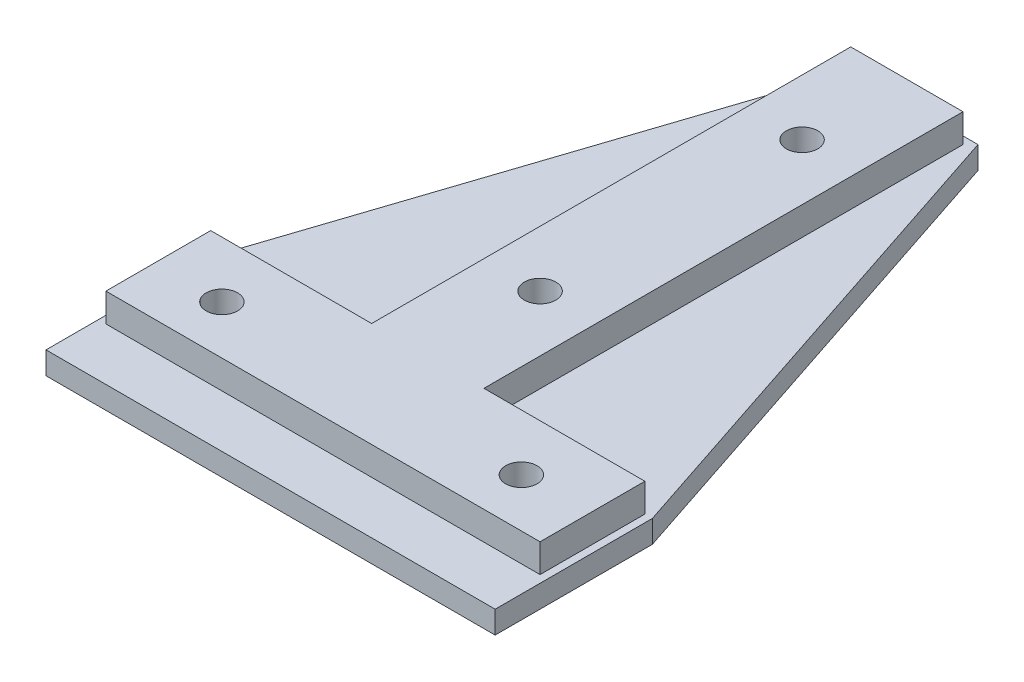
SolidWorks part; units mm, degrees
ref_plane "Front Plane" through (0, 0, 0) normal (0, 0, 1) x (1, 0, 0)
ref_plane "Top Plane" through (0, 0, 0) normal (0, 1, 0) x (1, 0, 0)
ref_plane "Right Plane" through (0, 0, 0) normal (1, 0, 0) x (0, 0, -1)
sketch "Sketch1" plane through (0, 0, 0) normal (0, 1, 0) x (1, 0, 0)
  line L0 (0, 7.5) -> (0, -50.0246) construction
  line L1 (-30, -7.5) -> (30, -7.5)
  line L2 (-30, -7.5) -> (-30, 7.5)
  line L3 (-30, 7.5) -> (30, 7.5)
  line L4 (30, -7.5) -> (30, 7.5)
  line L5 (-30, -7.5) -> (30, 7.5) construction
  line L6 (-30, 7.5) -> (30, -7.5) construction
  line L7 (-30, 0) -> (30, 0) construction
  line L8 (8.5, 7.5) -> (8.5, 72.5)
  line L9 (8.5, 7.5) -> (-8.5, 7.5)
  line L11 (8.5, 72.5) -> (-8.5, 72.5)
  line L12 (-8.5, 7.5) -> (-8.5, 72.5)
  line L13 (0, 72.5) -> (0, 7.5) construction
  line L14 (-8.5, 72.5) -> (-30, 7.5)
  line L15 (8.5, 72.5) -> (30, 7.5)
  line L17 (-30, -7.5) -> (30, -7.5)
  line L18 (-30, -7.5) -> (-30, -13.5)
  line L19 (-30, -13.5) -> (30, -13.5)
  line L20 (30, -7.5) -> (30, -13.5)
  circle A0 centre (-20, 0) radius 2.1
  circle A1 centre (20, 0) radius 2.1
  circle A2 centre (0, 57.5) radius 2.1
  circle A3 centre (0, 22.5) radius 2.1
  point P0 (0, 0)
  dimension "D3" = 4.2
  dimension "D4" = 10
  dimension "D6" = 4.2
  dimension "D7" = 15
  dimension "D8" = 4.2
  dimension "D9" = 15
  dimension "D1" = 60
  dimension "D2" = 15
  dimension "D5" = 65
  dimension "D10" = 6
extrude "Boss-Extrude1" add sketch "Sketch1" along normal blind 3 contours L12 L14 L3 | L15 L8 L3 | L12 L3 L8 L11 A3 A2 | L1 L4 L3 L2 A0 A1 | L20 L1 L18 L19 | A2 | A3 | A0 | A1
sketch "Sketch2" plane through (0, 3, 0) normal (0, 1, 0) x (1, 0, 0)
  line L1 (-30, 7.5) -> (30, 7.5)
  line L2 (-30, 7.5) -> (-30, -7.5)
  line L3 (-30, -7.5) -> (30, -7.5)
  line L4 (30, 7.5) -> (30, -7.5)
  line L5 (-8.5, 72.5) -> (8.5, 72.5)
  line L6 (-8.5, 72.5) -> (-8.5, 7.5)
  line L7 (-8.5, 7.5) -> (8.5, 7.5)
  line L8 (8.5, 72.5) -> (8.5, 7.5)
  circle A0 centre (0, 57.5) radius 2.1
  circle A1 centre (0, 22.5) radius 2.1
  circle A2 centre (-20, 0) radius 2.1
  circle A3 centre (20, 0) radius 2.1
  line M3 (8.5, 72.5) -> (-8.5, 72.5)
  line M5 (-30, 7.5) -> (-30, -13.5)
  line M7 (30, -13.5) -> (30, 7.5)
extrude "Boss-Extrude2" add sketch "Sketch2" along normal blind 3.8 contours L8 L6 L1 A1 A0 M3 | L3 L1 A3 A2 M5 M7
sketch "Sketch3" plane through (0, 6.8, 0) normal (0, 1, 0) x (1, 0, 0)
  circle A0 centre (0, 57.5) radius 2.1
  circle A1 centre (0, 22.5) radius 2.1
  circle A2 centre (20, 0) radius 2.1
  circle A3 centre (-20, 0) radius 2.1
extrude "Cut-Extrude1" cut sketch "Sketch3" against normal blind 18.8
sketch "Sketch4" plane through (0, 0, 0) normal (0, -1, 0) x (-1, 0, 0)
  line L0 (0, 22.5) -> (0, 57.5) construction
  line L2 (23.6, 2.1) -> (23.6, -2.1)
  line L4 (16.4, 2.1) -> (16.4, -2.1)
  line L5 (23.6, 2.1) -> (16.4, -2.1) construction
  line L6 (23.6, -2.1) -> (16.4, 2.1) construction
  line L7 (0, 20.4) -> (0, 18.4) construction
  line L8 (3.6, 22.5) -> (-3.6, 22.5) construction
  line L9 (0, 40) -> (-9.2444, 40) construction
  line L10 (20, -2.1) -> (20, -4.1) construction
  line L11 (20, -4.1) -> (23.6, -2.1)
  line L12 (16.4, -2.1) -> (20, -4.1)
  line L13 (23.6, 0) -> (16.4, 0) construction
  line L14 (16.4, 2.1) -> (20, 4.1)
  line L15 (20, 4.1) -> (23.6, 2.1)
  line L16 (-23.6, 2.1) -> (-23.6, -2.1)
  line L17 (-20, 4.1) -> (-23.6, 2.1)
  line L18 (-16.4, 2.1) -> (-20, 4.1)
  line L19 (-16.4, 2.1) -> (-16.4, -2.1)
  line L20 (-16.4, -2.1) -> (-20, -4.1)
  line L21 (-20, -4.1) -> (-23.6, -2.1)
  line L22 (0, 18.4) -> (3.6, 20.4)
  line L24 (3.6, 24.6) -> (3.6, 20.4)
  line L26 (-3.6, 24.6) -> (-3.6, 20.4)
  line L27 (3.6, 24.6) -> (-3.6, 20.4) construction
  line L28 (3.6, 20.4) -> (-3.6, 24.6) construction
  line L29 (0, 18.4) -> (-3.6, 20.4)
  line L30 (0, 26.6) -> (3.6, 24.6)
  line L31 (0, 26.6) -> (-3.6, 24.6)
  line L32 (3.6, 55.4) -> (3.6, 59.6)
  line L33 (0, 61.6) -> (3.6, 59.6)
  line L34 (0, 61.6) -> (-3.6, 59.6)
  line L35 (-3.6, 55.4) -> (-3.6, 59.6)
  line L36 (0, 53.4) -> (-3.6, 55.4)
  line L37 (0, 53.4) -> (3.6, 55.4)
  point P0 (20, 0)
  dimension "D1" = 7.2
  dimension "D2" = 4.2
  dimension "D3" = 2
  dimension "D4" = 7.2
  dimension "D5" = 4.2
  dimension "D6" = 2
extrude "Cut-Extrude2" cut sketch "Sketch4" against normal blind 3
sketch "Sketch5" plane through (0, 6.8, 0) normal (0, 1, 0) x (1, 0, 0)
  line L0 (-30, -7.5) -> (30, -7.5) construction
  line L1 (-30, 7.5) -> (-29, 7.5)
  line L2 (-30, 7.5) -> (-30, -7.5)
  line L3 (-30, -7.5) -> (-29, -7.5)
  line L4 (-29, 7.5) -> (-29, -7.5)
  line L5 (-30, -7.5) -> (30, -7.5) construction
  line L6 (30, 7.5) -> (29, 7.5)
  line L7 (30, 7.5) -> (30, -7.5)
  line L8 (30, -7.5) -> (29, -7.5)
  line L9 (29, 7.5) -> (29, -7.5)
  line L10 (8.5, 72.5) -> (8.5, 7.5) construction
  line L11 (-30, -7.5) -> (30, -7.5)
  line L12 (-30, -7.5) -> (-30, -6.5)
  line L13 (-30, -6.5) -> (30, -6.5)
  line L14 (30, -7.5) -> (30, -6.5)
  line L15 (-8.5, 72.5) -> (8.5, 72.5)
  line L16 (-8.5, 72.5) -> (-8.5, 71.5)
  line L17 (-8.5, 71.5) -> (8.5, 71.5)
  line L18 (8.5, 72.5) -> (8.5, 71.5)
  line L20 (-8.5, 72.5) -> (-7.5, 72.5)
  line L21 (-8.5, 72.5) -> (-8.5, 7.5)
  line L22 (-8.5, 7.5) -> (-7.5, 7.5)
  line L23 (-7.5, 72.5) -> (-7.5, 7.5)
  line L24 (8.5, 72.5) -> (7.5, 72.5)
  line L25 (8.5, 72.5) -> (8.5, 7.5)
  line L26 (8.5, 7.5) -> (7.5, 7.5)
  line L27 (7.5, 72.5) -> (7.5, 7.5)
  line M5 (8.5, 7.5) -> (8.5, 72.5)
  line M6 (8.5, 72.5) -> (-8.5, 72.5)
  line M7 (-8.5, 72.5) -> (-8.5, 7.5)
  line M8 (-8.5, 7.5) -> (-30, 7.5)
  line M9 (-30, 7.5) -> (-30, -7.5)
  line M10 (-30, -7.5) -> (30, -7.5)
  line M11 (30, -7.5) -> (30, 7.5)
  line M12 (30, 7.5) -> (8.5, 7.5)
  dimension "D1" = 1
  dimension "D2" = 1
  dimension "D3" = 1
  dimension "D4" = 1
  dimension "D5" = 1
  dimension "D6" = 1
extrude "Cut-Extrude3" cut sketch "Sketch5" against normal blind 3.8 contours L27 L17 M6 M5 | L27 L15 L23 L17 | L23 L15 L17 M7 | L23 L17 L22 M7 | L17 L27 L26 M5 | L13 L9 M10 M11 | L13 L2 L4 M10 | L13 L4 M9 M8 | L13 L4 L9 M10 | L9 L13 L7 M12
